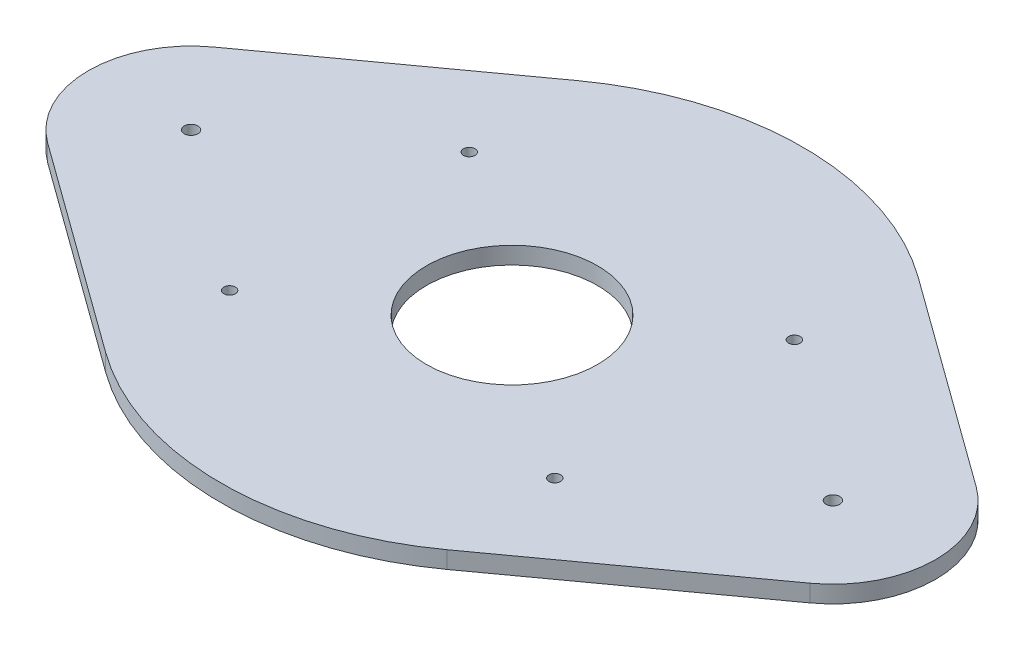
SolidWorks part; units mm, degrees
ref_plane "Alzado" through (0, 0, 0) normal (0, 0, 1) x (1, 0, 0)
ref_plane "Planta" through (0, 0, 0) normal (0, 1, 0) x (1, 0, 0)
ref_plane "Vista lateral" through (0, 0, 0) normal (1, 0, 0) x (0, 0, -1)
sketch "Croquis1" plane through (0, 0, 0) normal (0, 1, 0) x (1, 0, 0)
  line L0 (-187.5, 0) -> (187.5, 0) construction
  line L1 (-187.5, 60) -> (187.5, 60) construction
  line L2 (-187.5, -60) -> (187.5, -60) construction
  line L3 (-99.7333, 137.6708) -> (-222.7, 48.5897)
  line L4 (-222.7, -48.5897) -> (-99.7333, -137.6708)
  line L5 (222.7, -48.5897) -> (99.7333, -137.6708)
  line L6 (99.7333, 137.6708) -> (222.7, 48.5897)
  line L8 (-95, -70) -> (95, -70) construction
  line L9 (-95, -70) -> (-95, 70) construction
  line L10 (-95, 70) -> (95, 70) construction
  line L11 (95, -70) -> (95, 70) construction
  line L12 (-95, -70) -> (95, 70) construction
  line L13 (-95, 70) -> (95, -70) construction
  circle A0 centre (0, 0) radius 170 construction
  arc A1 (-187.5, 60) -> (-187.5, -60) centre (-187.5, 0) ccw construction
  arc A2 (187.5, -60) -> (187.5, 60) centre (187.5, 0) ccw construction
  arc A3 (99.7333, 137.6708) -> (-99.7333, 137.6708) centre (0, 0) ccw
  arc A4 (222.7, -48.5897) -> (222.7, 48.5897) centre (187.5, 0) ccw
  arc A5 (-222.7, -48.5897) -> (-222.7, 48.5897) centre (-187.5, 0) cw
  arc A6 (99.7333, -137.6708) -> (-99.7333, -137.6708) centre (0, 0) cw
  circle A7 centre (0, 0) radius 50
  circle A8 centre (-95, 70) radius 3.4
  circle A9 centre (95, 70) radius 3.4
  circle A10 centre (95, -70) radius 3.4
  circle A11 centre (-95, -70) radius 3.4
  circle A12 centre (187.5, 0) radius 4
  circle A13 centre (-187.5, 0) radius 4
  point P5 (0, 0)
  dimension "D1" = 340
  dimension "D3" = 60
  dimension "D4" = 100
  dimension "D7" = 6.8
  dimension "D8" = 6.8
  dimension "D9" = 6.8
  dimension "D10" = 6.8
  dimension "D11" = 8
  dimension "D12" = 8
  dimension "D2" = 375
  dimension "D5" = 190
  dimension "D6" = 140
extrude "Saliente-Extruir1" add sketch "Croquis1" along normal blind 10 contours A6 L5 A4 L6 A3 L3 A5 L4
